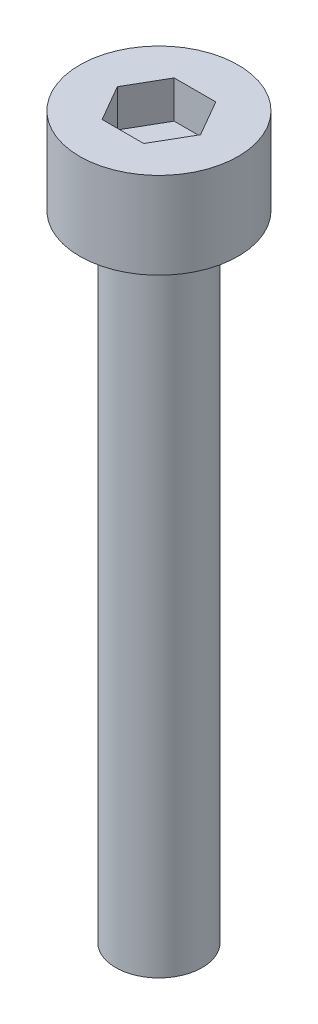
SolidWorks part; units mm, degrees
material "AISI 304"
ref_plane "前视基准面" through (0, 0, 0) normal (0, 0, 1) x (1, 0, 0)
ref_plane "上视基准面" through (0, 0, 0) normal (0, 1, 0) x (1, 0, 0)
ref_plane "右视基准面" through (0, 0, 0) normal (1, 0, 0) x (0, 0, -1)
sketch "草图1" plane through (0, 0, 0) normal (0, 1, 0) x (1, 0, 0)
  circle A0 centre (0, 0) radius 2.75
  dimension "D1" = 5.5
extrude "杯头" add sketch "草图1" along normal blind 3
sketch "草图2" plane through (0, 3, 0) normal (0, 1, 0) x (1, 0, 0)
  line L1 (1.4434, 0) -> (0.7217, 1.25)
  line L2 (0.7217, 1.25) -> (-0.7217, 1.25)
  line L3 (-0.7217, 1.25) -> (-1.4434, 0)
  line L4 (-1.4434, 0) -> (-0.7217, -1.25)
  line L5 (-0.7217, -1.25) -> (0.7217, -1.25)
  line L6 (0.7217, -1.25) -> (1.4434, 0)
  circle A0 centre (0, 0) radius 1.25 construction
  dimension "D1" = 2.5
extrude "内六角口" cut sketch "草图2" against normal blind 1.3
sketch "草图3" plane through (0, 0, 0) normal (0, -1, 0) x (1, 0, 0)
  circle A0 centre (0, 0) radius 1.5
  dimension "D1" = 3
extrude "螺纹长" add sketch "草图3" along normal blind 22
